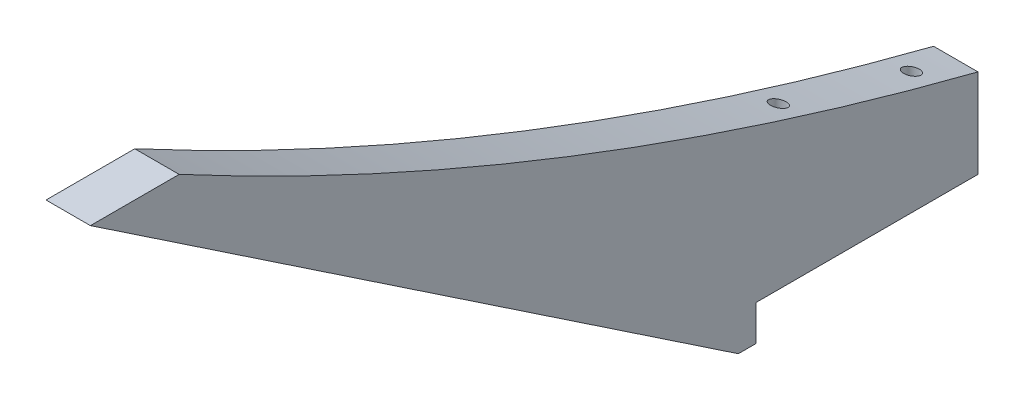
SolidWorks part; units mm, degrees
material "Delrin 2700 NC010, Low Viscosity Acetal Copolymer (SS)"
ref_plane "Front Plane" through (0, 0, 0) normal (0, 0, 1) x (1, 0, 0)
ref_plane "Top Plane" through (0, 0, 0) normal (0, 1, 0) x (1, 0, 0)
ref_plane "Right Plane" through (0, 0, 0) normal (1, 0, 0) x (0, 0, -1)
sketch "Sketch1" plane through (0, 0, 0) normal (1, 0, 0) x (0, 0, -1)
  line L0 (0, 0) -> (0, 12.7)
  line L1 (0, 12.7) -> (0, 57.15) construction
  line L2 (0, 57.15) -> (-127, 57.15) construction
  line L3 (0, 0) -> (-31.75, 0)
  line L5 (-127, 57.15) -> (-114.3, 57.15)
  line L8 (-31.75, 0) -> (-31.75, -5.08)
  line L9 (-31.75, -5.08) -> (-34.29, -5.08)
  line L10 (-34.29, -5.08) -> (-127, 57.15)
  arc A0 (-114.3, 57.15) -> (0, 12.7) centre (125.6264, 504.9215) ccw
  dimension "D9" = 508
  dimension "D1" = 127
  dimension "D2" = 44.45
  dimension "D3" = 12.7
  dimension "D4" = 12.7
  dimension "D5" = 5.08
  dimension "D7" = 2.54
  dimension "D8" = 31.75
extrude "Boss-Extrude1" add sketch "Sketch1" along normal blind 6.35
hole_wizard "#4-40 Tapped Hole1" positions "Sketch5" profile "Sketch6" tap size "#4-40" standard "ANSI Inch"
sketch "Sketch5" plane through (0, 0, 0) normal (0, -1, 0) x (-1, 0, 0)
  line L0 (-3.175, 0) -> (-3.175, -6.35) construction
  line L1 (-6.35, 0) -> (0, 0) construction
  line L2 (-3.175, -6.35) -> (-3.175, -25.4) construction
  line L3 (-3.175, -25.4) -> (-3.175, -31.75) construction
  line L4 (-6.35, -31.75) -> (0, -31.75) construction
  point P12 (-3.175, -25.4)
  point P14 (-3.175, -6.35)
  dimension "D1" = 19.05
  dimension "D2" = 6.35
sketch "Sketch6" plane through (3.175, 0, 25.4) normal (1, 0, 0) x (0, 0, -1)
  line L0 (0, 0) -> (0, 19.8905)
  line L1 (0, 19.8905) -> (1.1303, 19.8905)
  line L2 (1.1303, 19.8905) -> (1.1303, 0)
  line L5 (1.1303, 0) -> (0, 0)
  line L11 (0, -6.35) -> (0, 107.95) construction
  dimension "Thru Tap Drill Dia." = 2.2606
  dimension "Thru Tap Drill Depth" = 19.8905
cosmetic thread "Hole Thread1" parameters "D2"=2.8448
cosmetic thread "Hole Thread2" parameters "D2"=2.8448
other "Move Face1" [suppressed] parameters "D1"=0.0508
